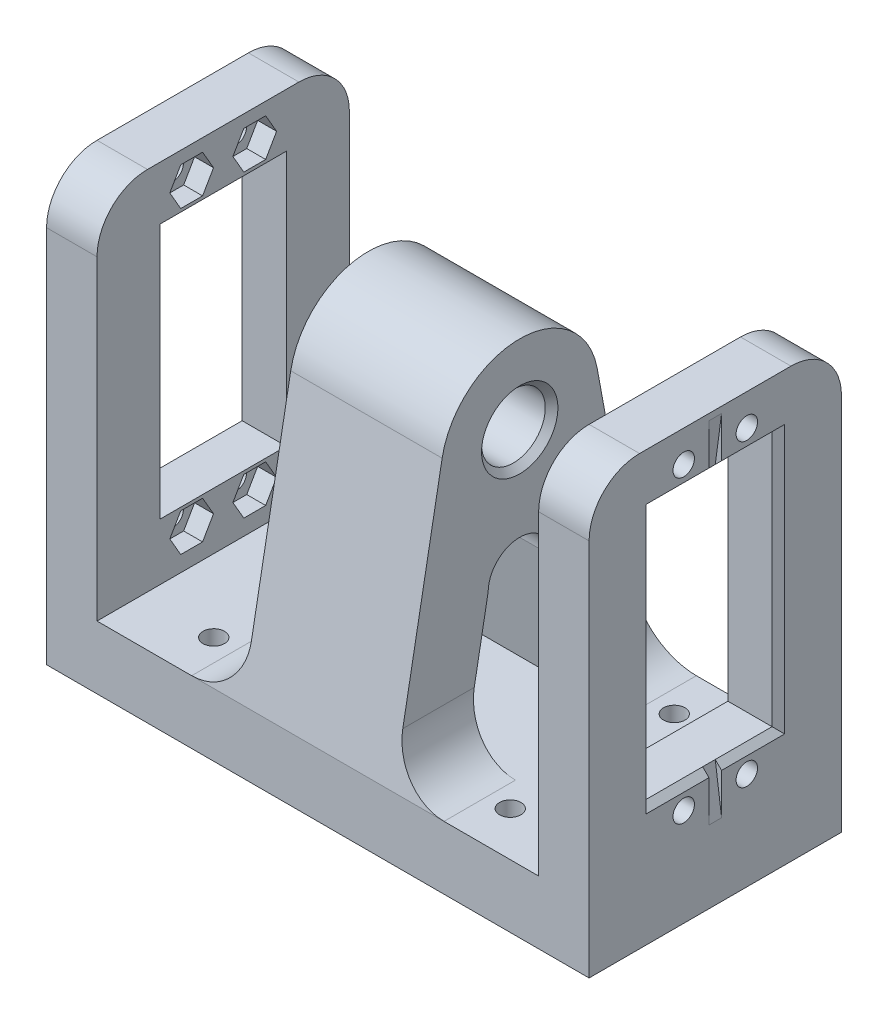
SolidWorks part; units mm, degrees
ref_plane "Спереди" through (0, 0, 0) normal (0, 0, 1) x (1, 0, 0)
ref_plane "Сверху" through (0, 0, 0) normal (0, 1, 0) x (1, 0, 0)
ref_plane "Справа" through (0, 0, 0) normal (1, 0, 0) x (0, 0, -1)
sketch "Эскиз1" plane through (0, 0, 0) normal (0, 0, 1) x (1, 0, 0)
  line L0 (0, 6.5894) -> (0, 0) construction
  line L1 (0, 0) -> (-43, 0) construction
  line L2 (0, 0) -> (16.6142, 0) construction
  line L4 (0, 0) -> (-12, 0)
  line L5 (0, 0) -> (0, 58)
  line L6 (0, 58) -> (-12, 58)
  line L7 (-12, 0) -> (-12, 58)
  line L8 (-43, 0) -> (-35, 0)
  line L9 (-43, 0) -> (-43, 58)
  line L10 (-43, 58) -> (-35, 58)
  line L11 (-35, 0) -> (-35, 58)
  line L12 (-43, 0) -> (0, 0)
  line L13 (-43, 0) -> (-43, -10)
  line L14 (-43, -10) -> (0, -10)
  line L15 (0, 0) -> (0, -10)
  dimension "D1" = 10
  dimension "D2" = 12
  dimension "D3" = 23
  dimension "D4" = 8
  dimension "D5" = 58
extrude "Бобышка-Вытянуть1" add sketch "Эскиз1" along normal mid plane 40 contours L15 L4 L12 L8 L13 L14 | L8 L11 L10 L9 | L7 L4 L5 L6
sketch "Эскиз3" plane through (-43, 0, 0) normal (-1, 0, 0) x (0, 0, 1)
  line L0 (0, 58) -> (0, -10) construction
  line L1 (20, 58) -> (-20, 58) construction
  line L2 (20, -10) -> (-20, -10) construction
  line L3 (-10, 29.25) -> (10, 29.25) construction
  line L4 (-10, 49.5) -> (10, 49.5)
  line L5 (-10, 49.5) -> (-10, 9)
  line L6 (-10, 9) -> (10, 9)
  line L7 (10, 49.5) -> (10, 9)
  circle A0 centre (0, 39.75) radius 5
  circle A1 centre (-5, 53) radius 1.7
  circle A2 centre (5, 53) radius 1.7
  circle A3 centre (-5, 5.5) radius 1.7
  circle A4 centre (5, 5.5) radius 1.7
  dimension "D5" = 3.4
  dimension "D9" = 10
  dimension "D1" = 20
  dimension "D2" = 40.5
  dimension "D3" = 9.75
  dimension "D4" = 3.5
  dimension "D6" = 5
  dimension "D7" = 10
  dimension "D8" = 18.25
extrude "Вырез-Серва" cut sketch "Эскиз3" against normal up to surface (8 mm away) contours L0 A0 | A0 L0 | L0 L4 L5 L6 A0 | L4 L0 A0 L6 L7 | A1 | A2 | A3 | A4
sketch "Эскиз2" plane through (-12, 0, 0) normal (-1, 0, 0) x (0, 0, 1)
  line L0 (0, 58) -> (0, 0) construction
  line L1 (-20, 0) -> (-12.2949, 42.0053)
  line L2 (20, 0) -> (12.2949, 42.0053)
  line L3 (8.6687, 0) -> (5, 20)
  line L4 (-20, 58) -> (-20, 0)
  line L5 (-20, 0) -> (20, 0)
  line L6 (20, 0) -> (20, 58)
  line L7 (20, 58) -> (-20, 58)
  line L8 (-20, 58) -> (-20, 0)
  line L9 (-20, 0) -> (20, 0)
  line L10 (20, 0) -> (20, 58)
  line L11 (20, 58) -> (-20, 58)
  line L12 (-8.6687, 0) -> (-5, 20)
  circle A0 centre (0, 39.75) radius 5.05
  circle A1 centre (0, 39.75) radius 12.5
  circle A2 centre (0, 20) radius 5
  line M8 (-20, 58) -> (-20, 0)
  line M9 (-20, 0) -> (20, 0)
  line M10 (20, 0) -> (20, 58)
  line M11 (20, 58) -> (-20, 58)
  dimension "D2" = 10.1
  dimension "D3" = 25
  dimension "D6" = 10
  dimension "D4" = 18.25
  dimension "D5" = 20
  dimension "D1" = 0
extrude "Вырез-Отверстие-Треуг" cut sketch "Эскиз2" against normal up to surface (12 mm away) contours L0 A1 L2 M11 M10 | L0 L11 L1 A1 M8 | A0 L0 | L0 A0 | L0 A2 L12 L9 | L0 A2 | A2 L0 | A2 L0 L3 M9
sketch "Эскиз4" plane through (0, 0, 0) normal (0, 0, 1) x (1, 0, 0)
  line L0 (-43, 49.5) -> (-43, 9) construction
  line L1 (-43, 49.5) -> (-43, 9)
  line L2 (-43, 49.5) -> (-43, 57)
  line L3 (-43, 57) -> (-42, 49.5)
  line L4 (-42, 49.5) -> (-43, 49.5)
  line L5 (-43, 29.25) -> (-19.3795, 29.25) construction
  line L6 (-43, 9) -> (-43, 1.5)
  line L7 (-42, 9) -> (-43, 9)
  line L8 (-43, 1.5) -> (-42, 9)
  dimension "D1" = 7.5
  dimension "D2" = 1
extrude "Вырез-Пазики серв" cut sketch "Эскиз4" against normal mid plane 2 contours L4 L3 L2 | L6 L8 L7
sketch "Эскиз5" plane through (-35, 0, 0) normal (1, 0, 0) x (0, 0, -1)
  line L1 (-6.7321, 56) -> (-8.4641, 53)
  line L2 (-8.4641, 53) -> (-6.7321, 50)
  line L3 (-6.7321, 50) -> (-3.2679, 50)
  line L4 (-3.2679, 50) -> (-1.5359, 53)
  line L5 (-1.5359, 53) -> (-3.2679, 56)
  line L6 (-3.2679, 56) -> (-6.7321, 56)
  line L7 (1.5359, 53) -> (3.2679, 50)
  line L8 (3.2679, 50) -> (6.7321, 50)
  line L9 (6.7321, 50) -> (8.4641, 53)
  line L10 (8.4641, 53) -> (6.7321, 56)
  line L11 (6.7321, 56) -> (3.2679, 56)
  line L12 (3.2679, 56) -> (1.5359, 53)
  line L13 (-6.7321, 8.5) -> (-8.4641, 5.5)
  line L14 (-8.4641, 5.5) -> (-6.7321, 2.5)
  line L15 (-6.7321, 2.5) -> (-3.2679, 2.5)
  line L16 (-3.2679, 2.5) -> (-1.5359, 5.5)
  line L17 (-1.5359, 5.5) -> (-3.2679, 8.5)
  line L18 (-3.2679, 8.5) -> (-6.7321, 8.5)
  line L19 (1.5359, 5.5) -> (3.2679, 2.5)
  line L20 (3.2679, 2.5) -> (6.7321, 2.5)
  line L21 (6.7321, 2.5) -> (8.4641, 5.5)
  line L22 (8.4641, 5.5) -> (6.7321, 8.5)
  line L23 (6.7321, 8.5) -> (3.2679, 8.5)
  line L24 (3.2679, 8.5) -> (1.5359, 5.5)
  circle A0 centre (-5, 53) radius 1.7 construction
  circle A1 centre (-5, 53) radius 1.7
  circle A2 centre (5, 53) radius 1.7 construction
  circle A3 centre (5, 53) radius 1.7
  circle A4 centre (-5, 5.5) radius 1.7 construction
  circle A5 centre (-5, 5.5) radius 1.7
  circle A6 centre (5, 5.5) radius 1.7 construction
  circle A7 centre (5, 5.5) radius 1.7
  circle A8 centre (-5, 53) radius 3 construction
  circle A9 centre (5, 53) radius 3 construction
  circle A10 centre (-5, 5.5) radius 3 construction
  circle A11 centre (5, 5.5) radius 3 construction
  dimension "D1" = 6
extrude "Вырез-Гайки" cut sketch "Эскиз5" against normal blind 3
sketch "Эскиз6" plane through (0, 0, 0) normal (0, 1, 0) x (1, 0, 0)
  line L0 (-23.5, 20) -> (-23.5, -20) construction
  line L1 (-35, 0) -> (0, 0) construction
  line L8 (-12, 20) -> (-35, 20)
  line L9 (-35, 20) -> (-35, -20)
  line L10 (-35, -20) -> (-12, -20)
  line L11 (-12, -20) -> (-12, -8.6687)
  line L12 (-12, -8.6687) -> (0, -8.6687)
  line L13 (0, -8.6687) -> (0, 8.6687)
  line L14 (0, 8.6687) -> (-12, 8.6687)
  line L15 (-12, 8.6687) -> (-12, 20)
  line L16 (-12, 20) -> (-35, 20)
  line L17 (-35, 20) -> (-35, -20)
  line L18 (-35, -20) -> (-12, -20)
  line L19 (-12, -20) -> (-12, -8.6687)
  line L20 (-12, -8.6687) -> (0, -8.6687)
  line L21 (0, -8.6687) -> (0, 8.6687)
  line L22 (0, 8.6687) -> (-12, 8.6687)
  line L23 (-12, 8.6687) -> (-12, 20)
  circle A0 centre (-23.5, 13) radius 1.7
  circle A1 centre (-23.5, -13) radius 1.7
  dimension "D2" = 3.4
  dimension "D3" = 26
  dimension "D1" = 0
extrude "Вырез-Вытянуть5" cut sketch "Эскиз6" against normal up to surface (10 mm away) contours A0 | A1 up to face at (-21.5, -10, 0)
fillet "Скругление1" radius 8 4 edges at (-12, 0, 14.3343) (-12, 0, -14.3343) (-39, 58, -20) (-39, 58, 20)
fillet "Скругление2" [suppressed] radius 2
chamfer "Фаска1" distance 1 angle 45 7 edges at (-12, 39.75, 5.05) (-43, 9, 5.5) (-43, 49.5, 5.5) (-43, 29.25, 10) (-43, 9, -5.5) (-43, 49.5, -5.5) (-43, 29.25, -10)
mirror "Зеркальное отражение2"
